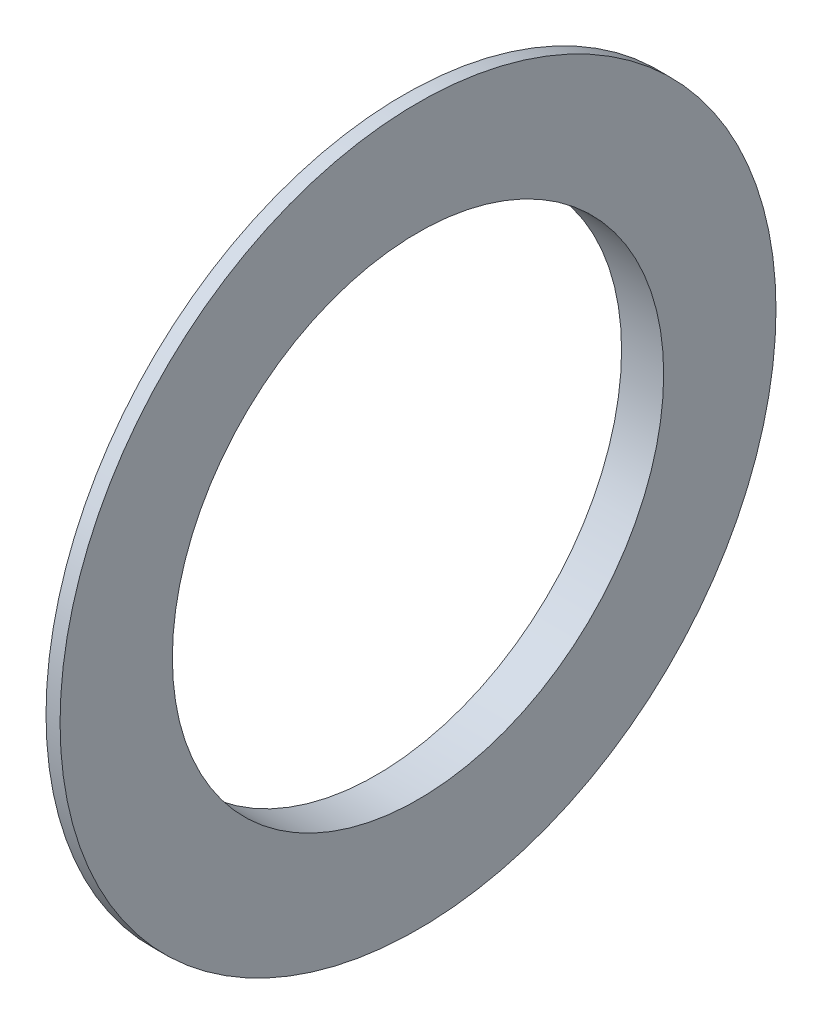
SolidWorks part; units mm, degrees
ref_plane "Płaszczyzna przednia" through (0, 0, 0) normal (0, 0, 1) x (1, 0, 0)
ref_plane "Płaszczyzna górna" through (0, 0, 0) normal (0, 1, 0) x (1, 0, 0)
ref_plane "Płaszczyzna prawa" through (0, 0, 0) normal (1, 0, 0) x (0, 0, -1)
sketch "Szkic1" plane through (0, 0, 0) normal (0, 0, 1) x (1, 0, 0)
  line L0 (86.7512, 19.0636) -> (86.7512, 17.5)
  line L1 (86.7512, 17.5) -> (89.7512, 17.5)
  line L2 (153.3423, 17.5) -> (86.7512, 17.5) construction
  line L3 (89.7512, 17.5) -> (89.7512, 25.5)
  line L4 (88.7512, 25.5) -> (86.7512, 19.0636)
  line L5 (88.7512, 25.5) -> (89.7512, 25.5)
  line L6 (0, 0) -> (109.1332, 0) construction
  dimension "D1" = 1
  dimension "D2" = 3
  dimension "D3" = 51
revolve "Obrót1" add sketch "Szkic1" angle 360 about L6
